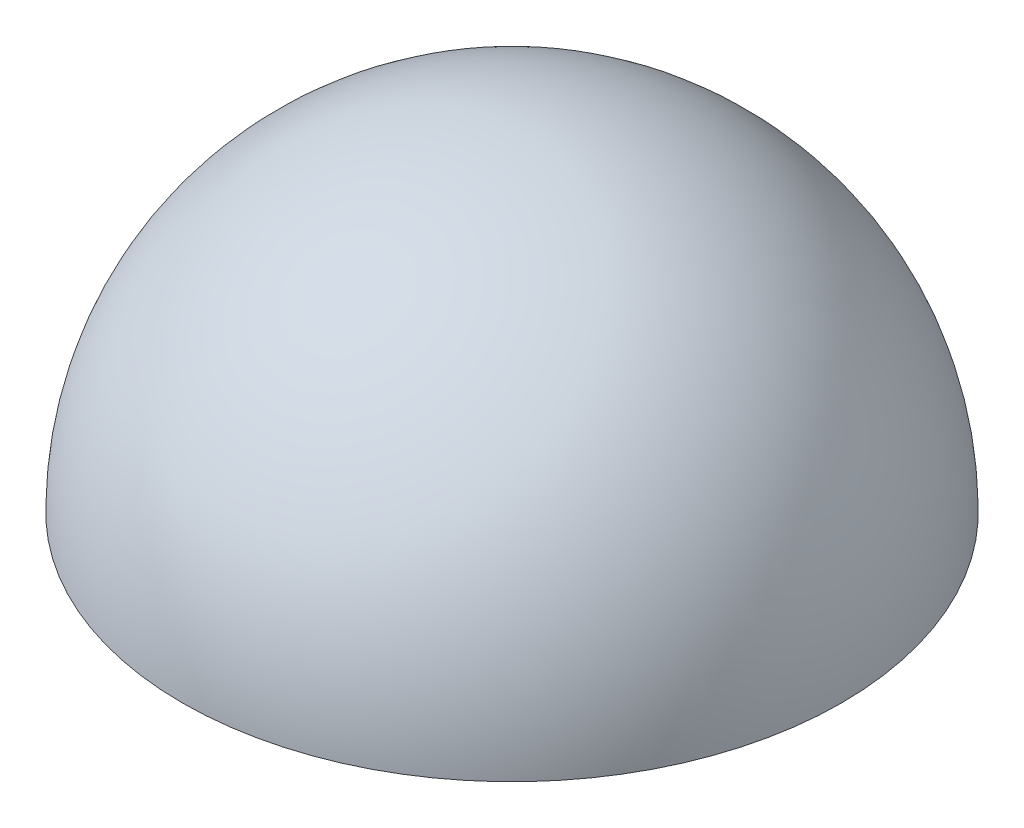
SolidWorks part; units mm, degrees
ref_plane "Front Plane" through (0, 0, 0) normal (0, 0, 1) x (1, 0, 0)
ref_plane "Top Plane" through (0, 0, 0) normal (0, 1, 0) x (1, 0, 0)
ref_plane "Right Plane" through (0, 0, 0) normal (1, 0, 0) x (0, 0, -1)
sketch "Sketch1" plane through (0, 0, 0) normal (0, 0, 1) x (1, 0, 0)
  line L0 (0, 8.4) -> (0, 9)
  line L1 (9, 0) -> (8.4, 0)
  arc A0 (8.4, 0) -> (0, 8.4) centre (0, 0) ccw
  arc A1 (9, 0) -> (0, 9) centre (0, 0) ccw
  dimension "D1" = 8.4
  dimension "D2" = 9
sketch "Sketch2" plane through (0, 0, 0) normal (0, 0, 1) x (1, 0, 0)
  line L0 (0, 8.3) -> (0, 0)
  line L1 (0, 0) -> (8.3, 0)
  arc A0 (8.3, 0) -> (0, 8.3) centre (0, 0) ccw
  dimension "D1" = 8.3
  dimension "D2" = 8.3
revolve "Revolve1" add sketch "Sketch1" angle 360 about L0
revolve "Revolve2" add sketch "Sketch2" angle 360 about L0
